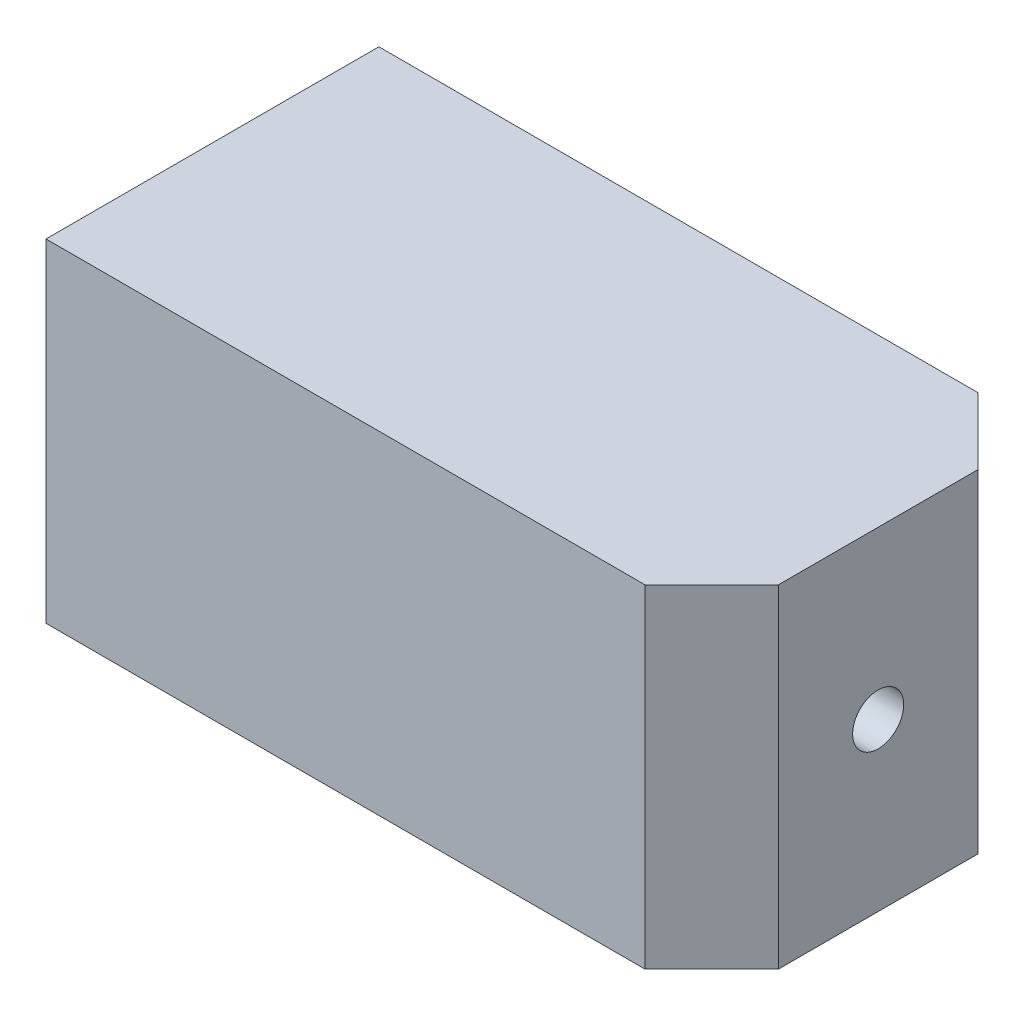
SolidWorks part; units mm, degrees
ref_plane "Front Plane" through (0, 0, 0) normal (0, 0, 1) x (1, 0, 0)
ref_plane "Top Plane" through (0, 0, 0) normal (0, 1, 0) x (1, 0, 0)
ref_plane "Right Plane" through (0, 0, 0) normal (1, 0, 0) x (0, 0, -1)
sketch "Sketch1" plane through (0, 0, 0) normal (0, 1, 0) x (1, 0, 0)
  line L1 (-15, 7.5) -> (15, 7.5)
  line L2 (-15, 7.5) -> (-15, -7.5)
  line L3 (-15, -7.5) -> (15, -7.5)
  line L4 (15, 7.5) -> (15, -7.5)
  line L5 (-15, 7.5) -> (15, -7.5) construction
  line L6 (-15, -7.5) -> (15, 7.5) construction
  point P0 (0, 0)
extrude "Boss-Extrude1" add sketch "Sketch1" along normal blind 15
chamfer "Chamfer1" distance 3 angle 45 2 edges at (15, 7.5, -7.5) (15, 7.5, 7.5)
sketch "Sketch2" plane through (-15, 0, 0) normal (-1, 0, 0) x (0, 0, 1)
  line L0 (0, 15) -> (0, 0) construction
  line L1 (-7.5, 15) -> (7.5, 15) construction
  line L2 (-7.5, 0) -> (7.5, 0) construction
  circle A0 centre (0, 7.5) radius 5
extrude "Cut-Extrude1" cut sketch "Sketch2" against normal offset from surface (27 mm away) 3 up to face at (15, 7.5, 0)
sketch "Sketch3" plane through (12, 0, 0) normal (-1, 0, 0) x (0, 0, 1)
  circle A0 centre (0, 7.5) radius 1.15
extrude "Cut-Extrude2" cut sketch "Sketch3" against normal blind 7
